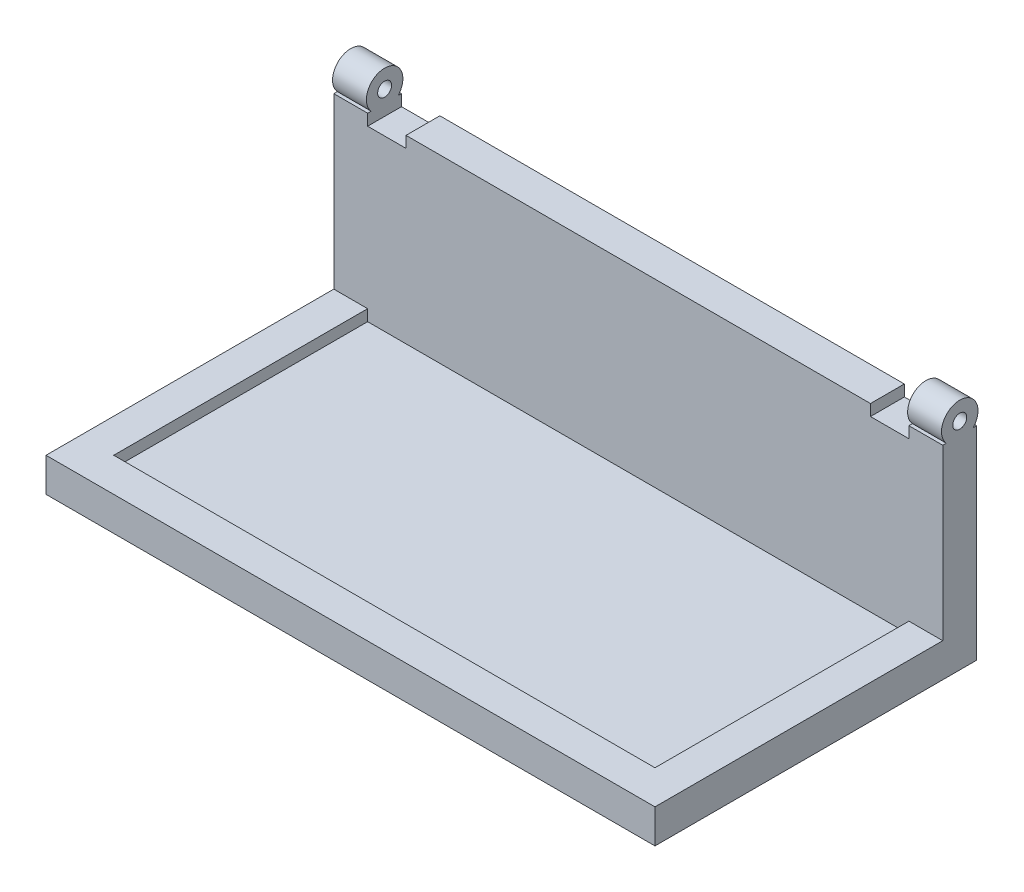
SolidWorks part; units mm, degrees
ref_plane "Front" through (0, 0, 0) normal (0, 0, 1) x (1, 0, 0)
ref_plane "Top" through (0, 0, 0) normal (0, 1, 0) x (1, 0, 0)
ref_plane "Right" through (0, 0, 0) normal (1, 0, 0) x (0, 0, -1)
sketch "Sketch1" plane through (0, 0, 0) normal (0, 1, 0) x (1, 0, 0)
  line L0 (-158.2084, -58.9575) -> (-158.2084, 83.5425)
  line L5 (-158.2084, 83.5425) -> (111.5916, 83.5425)
  line L6 (111.5916, -58.9575) -> (111.5916, 83.5425)
  line L7 (-158.2084, -58.9575) -> (111.5916, -58.9575)
extrude "Boss-Extrude2" add sketch "Sketch1" along normal blind 15
sketch "Sketch2" plane through (0, 15, 0) normal (0, 1, 0) x (1, 0, 0)
  line L8 (-143.2084, -43.9575) -> (96.5916, -43.9575)
  line L9 (96.5916, -43.9575) -> (96.5916, 68.5425)
  line L10 (96.5916, 68.5425) -> (-143.2084, 68.5425)
  line L11 (-143.2084, 68.5425) -> (-143.2084, -43.9575)
  line L12 (-143.2084, -43.9575) -> (96.5916, -43.9575)
  line L13 (96.5916, -43.9575) -> (96.5916, 68.5425)
  line L14 (96.5916, 68.5425) -> (-143.2084, 68.5425)
  line L15 (-143.2084, 68.5425) -> (-143.2084, -43.9575)
  dimension "D1" = 15
extrude "Cut-Extrude1" cut sketch "Sketch2" against normal blind 5
sketch "Sketch3" plane through (0, 15, 0) normal (0, 1, 0) x (1, 0, 0)
  line L0 (-143.2084, 68.5425) -> (-158.2084, 68.5425)
  line L1 (-158.2084, 83.5425) -> (-158.2084, -58.9575) construction
  line L2 (-143.2084, 68.5425) -> (111.5916, 68.5425)
  line L3 (111.5916, -58.9575) -> (111.5916, 83.5425) construction
  line L4 (111.5916, 68.5425) -> (111.5916, 83.5425)
  line L5 (111.5916, 83.5425) -> (-158.2084, 83.5425)
  line L6 (-158.2084, 83.5425) -> (-158.2084, 68.5425)
extrude "Boss-Extrude3" add sketch "Sketch3" along normal blind 75
sketch "Sketch4" plane through (0, 90, 0) normal (0, 1, 0) x (1, 0, 0)
  line L0 (-143.2084, 68.5425) -> (-143.2084, 83.5425) construction
  line L1 (111.5916, 83.5425) -> (-158.2084, 83.5425) construction
  line L2 (-143.2084, 83.5425) -> (-158.2084, 83.5425) construction
  line L3 (-158.2084, 83.5425) -> (-158.2084, 68.5425) construction
  line L4 (-158.2084, 68.5425) -> (-143.2084, 68.5425) construction
  line L5 (111.5916, 68.5425) -> (111.5916, 83.5425) construction
  line L6 (111.5916, 83.5425) -> (96.5916, 83.5425) construction
  line L7 (96.5916, 83.5425) -> (96.5916, 68.5425) construction
  line L8 (96.5916, 68.5425) -> (111.5916, 68.5425) construction
  line L9 (-143.2084, 83.5425) -> (-128.2084, 83.5425) construction
  line L10 (-128.2084, 83.5425) -> (-128.2084, 68.5425) construction
  line L11 (-158.2084, 68.5425) -> (111.5916, 68.5425) construction
  line L12 (-128.2084, 68.5425) -> (-143.2084, 68.5425) construction
  line L13 (96.5916, 83.5425) -> (81.5916, 83.5425) construction
  line L14 (81.5916, 83.5425) -> (81.5916, 68.5425) construction
  line L15 (96.5916, 68.5425) -> (-143.2084, 68.5425) construction
  line L16 (81.5916, 68.5425) -> (96.5916, 68.5425) construction
  dimension "D1" = 15
  dimension "D2" = 15
  dimension "D3" = 15
ref_plane "Plane3" through (-143.2084, 0, 0) normal (1, 0, 0) x (0, 0, -1)
ref_plane "Plane4" through (96.5916, 0, 0) normal (-1, 0, 0) x (0, 0, 1)
sketch "Sketch7" plane through (-143.2084, 0, 0) normal (1, 0, 0) x (0, 0, -1)
  line L0 (84.3883, 95.4538) -> (67.7537, 95.4538) construction
  line L1 (76.071, 86.8252) -> (76.071, 104.0825) construction
  circle A2 centre (76.071, 95.4538) radius 8.0891
  circle A3 centre (76.071, 95.4538) radius 3.0891
  point P9 (76.071, 95.4538)
  dimension "D1" = 5
sketch "Sketch12" plane through (96.5916, 0, 0) normal (-1, 0, 0) x (0, 0, 1)
  circle A0 centre (-76.071, 95.4538) radius 8.0891 construction
  circle A1 centre (-76.071, 95.4538) radius 3.0891 construction
  circle A2 centre (-76.071, 95.4538) radius 8.0891
  circle A3 centre (-76.071, 95.4538) radius 3.0891
sketch "Sketch13" plane through (96.5916, 0, 0) normal (-1, 0, 0) x (0, 0, 1)
  line L0 (-84.3883, 95.4538) -> (-67.7537, 95.4538) construction
  line L1 (-84.3883, 95.4538) -> (-67.7537, 95.4538)
extrude "Boss-Extrude4" add sketch "Sketch7" against normal blind 15
extrude "Boss-Extrude5" add sketch "Sketch12" against normal blind 15
sketch "Sketch14" plane through (0, 90, 0) normal (0, 1, 0) x (1, 0, 0)
  line L0 (-128.2084, 83.5425) -> (-143.2084, 83.5425)
  line L1 (-143.2084, 83.5425) -> (-143.2084, 68.5425)
  line L2 (-143.2084, 68.5425) -> (-128.2084, 68.5425)
  line L3 (-128.2084, 68.5425) -> (-126.2084, 68.5425)
  line L4 (96.5916, 68.5425) -> (-143.2084, 68.5425) construction
  line L5 (-126.2084, 68.5425) -> (-126.2084, 83.5425)
  line L6 (111.5916, 83.5425) -> (-158.2084, 83.5425) construction
  line L7 (-126.2084, 83.5425) -> (-128.2084, 83.5425)
  line L8 (96.5916, 83.5425) -> (79.5689, 83.5425)
  line L9 (79.5689, 83.5425) -> (79.5689, 68.5425)
  line L10 (-158.2084, 68.5425) -> (111.5916, 68.5425) construction
  line L11 (79.5689, 68.5425) -> (96.5916, 68.5425)
  line L12 (95.1699, 68.5425) -> (96.5916, 68.5425)
  line L13 (96.5916, 68.5425) -> (96.5916, 83.5425)
  line M13 (111.5916, 83.5425) -> (-158.2084, 83.5425)
  line M16 (-143.2084, 82.045) -> (-143.2084, 70.097)
  line M19 (-158.2084, 68.5425) -> (111.5916, 68.5425)
  dimension "D1" = 2
extrude "Cut-Extrude2" cut sketch "Sketch14" against normal blind 5 contours L5 L1 M19 M13 M16 | L13 L8 L9 L11
